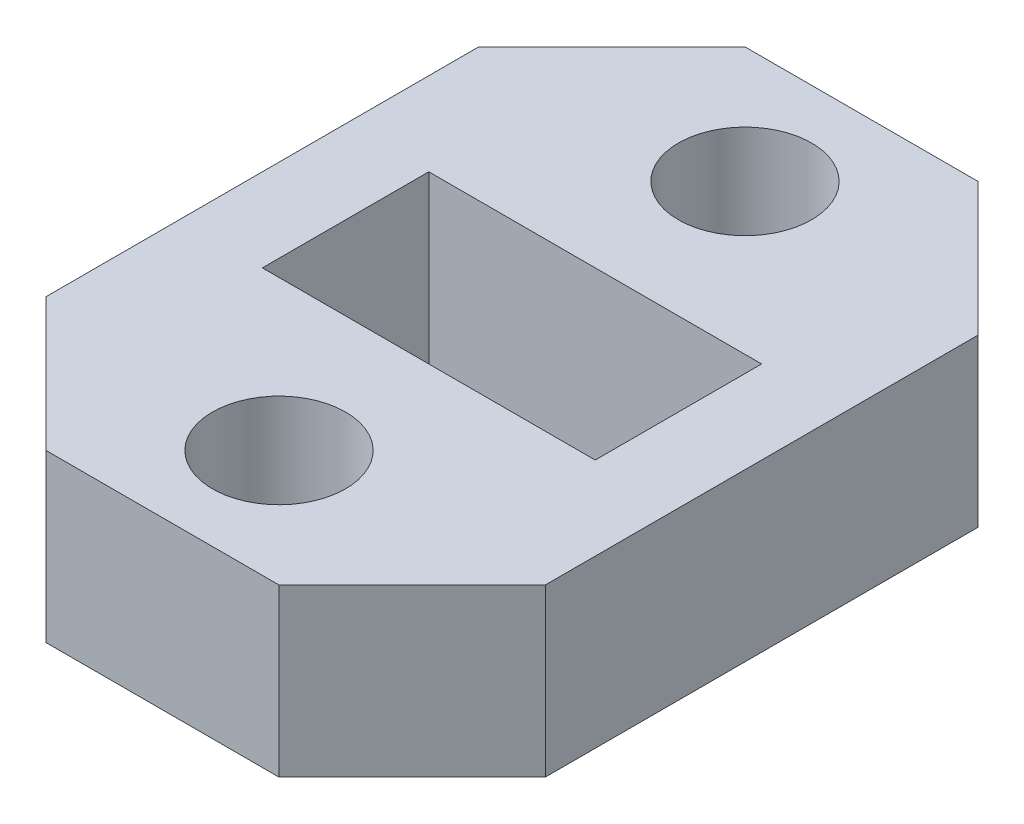
SolidWorks part; units mm, degrees
material "Acrylic (Medium-high impact)"
ref_plane "Front Plane" through (0, 0, 0) normal (0, 0, 1) x (1, 0, 0)
ref_plane "Top Plane" through (0, 0, 0) normal (0, 1, 0) x (1, 0, 0)
ref_plane "Right Plane" through (0, 0, 0) normal (1, 0, 0) x (0, 0, -1)
sketch "Sketch1" plane through (0, 0, 0) normal (0, 1, 0) x (1, 0, 0)
  line L1 (-7.5, -10.5) -> (7.5, -10.5)
  line L2 (-7.5, -10.5) -> (-7.5, 10.5)
  line L3 (-7.5, 10.5) -> (7.5, 10.5)
  line L4 (7.5, -10.5) -> (7.5, 10.5)
  line L5 (-7.5, -10.5) -> (7.5, 10.5) construction
  line L6 (-7.5, 10.5) -> (7.5, -10.5) construction
  point P0 (0, 0)
  dimension "D1" = 15
  dimension "D2" = 21
extrude "Boss-Extrude1" add sketch "Sketch1" along normal blind 5
sketch "Sketch2" plane through (0, 5, 0) normal (0, 1, 0) x (1, 0, 0)
  line L1 (-5, -2.5) -> (5, -2.5)
  line L2 (-5, -2.5) -> (-5, 2.5)
  line L3 (-5, 2.5) -> (5, 2.5)
  line L4 (5, -2.5) -> (5, 2.5)
  line L5 (-5, -2.5) -> (5, 2.5) construction
  line L6 (-5, 2.5) -> (5, -2.5) construction
  line L7 (0, 0) -> (5, 0) construction
  circle A0 centre (0, 7) radius 2
  circle A1 centre (0, -7) radius 2
  point P0 (0, 0)
  dimension "D4" = 4
  dimension "D1" = 5
  dimension "D2" = 10
  dimension "D5" = 7
extrude "Cut-Extrude1" cut sketch "Sketch2" against normal blind 5
chamfer "Chamfer1" distance 4 angle 45 4 edges at (-7.5, 2.5, 10.5) (7.5, 2.5, 10.5) (7.5, 2.5, -10.5) (-7.5, 2.5, -10.5)
